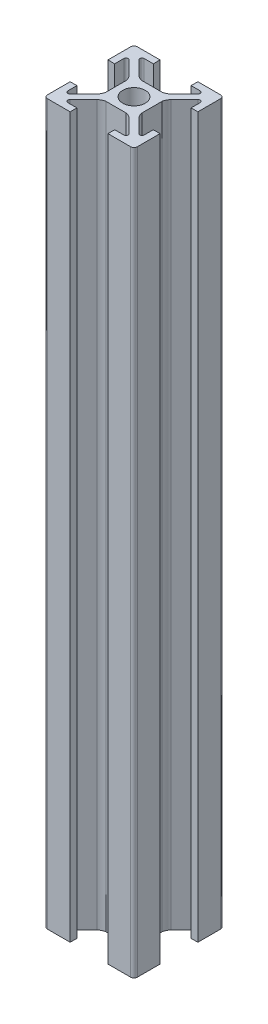
SolidWorks part; units mm, degrees
ref_plane "Front Plane" through (0, 0, 0) normal (0, 0, 1) x (1, 0, 0)
ref_plane "Top Plane" through (0, 0, 0) normal (0, 1, 0) x (1, 0, 0)
ref_plane "Right Plane" through (0, 0, 0) normal (1, 0, 0) x (0, 0, -1)
sketch "Sketch1" plane through (0, 0, 0) normal (0, 1, 0) x (1, 0, 0)
  line L0 (-3.611, 4.6716) -> (-6.5858, 7.6464)
  line L1 (9.25, -10) -> (4.2, -10)
  line L2 (10, -9.25) -> (10, -4.2)
  line L3 (9.25, 10) -> (4.2, 10)
  line L4 (-10, -9.25) -> (-10, -4.2)
  line L5 (10, -10) -> (-10, 10) construction
  line L6 (10, 10) -> (-10, -10) construction
  line L7 (2.2681, -4) -> (-2.2681, -4)
  line L8 (4, -2.2681) -> (4, 2.2681)
  line L9 (2.2681, 4) -> (-2.2681, 4)
  line L10 (-4, -2.2681) -> (-4, 2.2681)
  line L11 (4, -4) -> (-4, 4) construction
  line L12 (4, 4) -> (-4, -4) construction
  line L13 (-6.2322, 8.5) -> (-4.2, 8.5)
  line L14 (-4.2, 8.5) -> (-4.2, 10)
  line L15 (4.6716, 3.611) -> (7.6464, 6.5858)
  line L16 (8.5, 6.2322) -> (8.5, 4.2)
  line L17 (8.5, 4.2) -> (10, 4.2)
  line L18 (4.2, 8.5) -> (4.2, 10)
  line L19 (-8.5, 4.2) -> (-10, 4.2)
  line L20 (-8.5, 6.2322) -> (-8.5, 4.2)
  line L21 (-4.6716, 3.611) -> (-7.6464, 6.5858)
  line L22 (0, 10) -> (0, -10) construction
  line L23 (6.2322, 8.5) -> (4.2, 8.5)
  line L24 (3.611, 4.6716) -> (6.5858, 7.6464)
  line L25 (-55, 0) -> (55, 0) construction
  line L26 (3.611, -4.6716) -> (6.5858, -7.6464)
  line L27 (6.2322, -8.5) -> (4.2, -8.5)
  line L28 (-4.6716, -3.611) -> (-7.6464, -6.5858)
  line L29 (-8.5, -6.2322) -> (-8.5, -4.2)
  line L30 (-8.5, -4.2) -> (-10, -4.2)
  line L31 (4.2, -8.5) -> (4.2, -10)
  line L32 (8.5, -4.2) -> (10, -4.2)
  line L33 (8.5, -6.2322) -> (8.5, -4.2)
  line L34 (4.6716, -3.611) -> (7.6464, -6.5858)
  line L35 (-4.2, -8.5) -> (-4.2, -10)
  line L36 (-6.2322, -8.5) -> (-4.2, -8.5)
  line L37 (2.2681, -4) -> (-2.2681, -4)
  line L38 (10, -10) -> (4.2, -10)
  line L39 (-3.611, -4.6716) -> (-6.5858, -7.6464)
  line L40 (-4.2, 10) -> (-9.25, 10)
  line L41 (-10, 4.2) -> (-10, 9.25)
  line L42 (-4.2, -10) -> (-9.25, -10)
  line L43 (-4.2, -10) -> (-10, -10)
  line L44 (10, 4.2) -> (10, 9.25)
  circle A0 centre (0, 0) radius 2.5
  arc A1 (-8.5, 6.2322) -> (-7.6464, 6.5858) centre (-8, 6.2322) cw
  arc A2 (-6.5858, 7.6464) -> (-6.2322, 8.5) centre (-6.2322, 8) cw
  arc A3 (-3.611, 4.6716) -> (-2.2681, 4) centre (-1.7294, 6.7555) ccw
  arc A4 (-4.6716, 3.611) -> (-4, 2.2681) centre (-6.7555, 1.7294) cw
  arc A5 (4.6716, 3.611) -> (4, 2.2681) centre (6.7555, 1.7294) ccw
  arc A6 (3.611, 4.6716) -> (2.2681, 4) centre (1.7294, 6.7555) cw
  arc A7 (6.5858, 7.6464) -> (6.2322, 8.5) centre (6.2322, 8) ccw
  arc A8 (8.5, 6.2322) -> (7.6464, 6.5858) centre (8, 6.2322) ccw
  arc A9 (8.5, -6.2322) -> (7.6464, -6.5858) centre (8, -6.2322) cw
  arc A10 (6.5858, -7.6464) -> (6.2322, -8.5) centre (6.2322, -8) cw
  arc A11 (3.611, -4.6716) -> (2.2681, -4) centre (1.7294, -6.7555) ccw
  arc A12 (4.6716, -3.611) -> (4, -2.2681) centre (6.7555, -1.7294) cw
  arc A13 (-4.6716, -3.611) -> (-4, -2.2681) centre (-6.7555, -1.7294) ccw
  arc A14 (-3.611, -4.6716) -> (-2.2681, -4) centre (-1.7294, -6.7555) cw
  arc A15 (-6.5858, -7.6464) -> (-6.2322, -8.5) centre (-6.2322, -8) ccw
  arc A16 (-8.5, -6.2322) -> (-7.6464, -6.5858) centre (-8, -6.2322) ccw
  arc A17 (-9.25, -10) -> (-10, -9.25) centre (-9.25, -9.25) cw
  arc A18 (9.25, -10) -> (10, -9.25) centre (9.25, -9.25) ccw
  arc A19 (10, 9.25) -> (9.25, 10) centre (9.25, 9.25) ccw
  arc A20 (-9.25, 10) -> (-10, 9.25) centre (-9.25, 9.25) ccw
  point P0 (0, 0)
  point P18 (-8.5, 7.4393)
  point P24 (-7.4393, 8.5)
  point P50 (7.4393, 8.5)
  point P51 (8.5, 7.4393)
  point P86 (8.5, -7.4393)
  point P87 (7.4393, -8.5)
  point P88 (-7.4393, -8.5)
  point P89 (-8.5, -7.4393)
  dimension "D2" = 5
  dimension "D7" = 0.5
  dimension "D8" = 0.75
  dimension "D1" = 20
  dimension "D3" = 8
  dimension "D4" = 1.5
  dimension "D5" = 1.5
  dimension "D6" = 8.4
extrude "Boss-Extrude1" add sketch "Sketch1" along normal blind 160 contours L40 A20 L41 L19 L20 A1 L21 A4 L10 A13 L28 A16 L29 L30 L4 A17 L42 L35 L36 A15 L39 A14 L7 A11 L26 A10 L27 L31 L1 A18 L2 L32 L33 A9 L34 A12 L8 A5 L15 A8 L16 L17 L44 A19 L3 L18 L23 A7 L24 A6 L9
